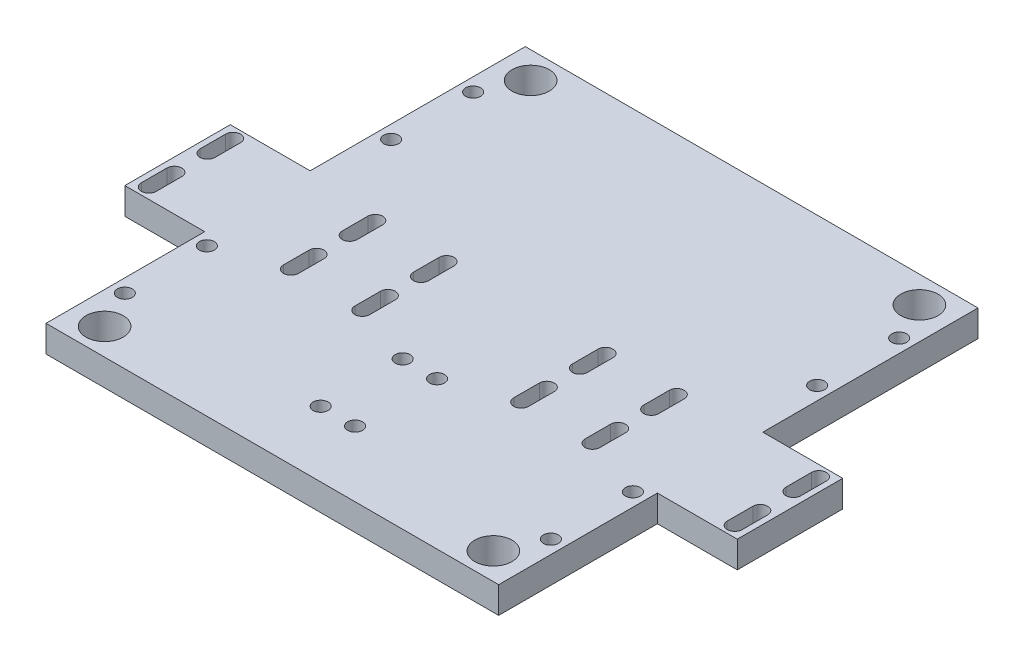
SolidWorks part; units mm, degrees
material "ABS"
ref_plane "Front Plane" through (0, 0, 0) normal (0, 0, 1) x (1, 0, 0)
ref_plane "Top Plane" through (0, 0, 0) normal (0, 1, 0) x (1, 0, 0)
ref_plane "Right Plane" through (0, 0, 0) normal (1, 0, 0) x (0, 0, -1)
sketch "Esquisse1" plane through (0, 0, 0) normal (0, 1, 0) x (1, 0, 0)
  line L0 (0, 0) -> (53.975, 0)
  line L1 (0, 0) -> (0, -114.3)
  line L2 (53.975, 0) -> (53.975, -51.308)
  line L3 (0, -114.3) -> (53.975, -114.3)
  line L4 (53.975, -76.454) -> (53.975, -114.3)
  line L5 (53.975, -51.308) -> (73.025, -51.308)
  line L7 (53.975, -76.454) -> (73.025, -76.454)
  line L8 (73.025, -51.308) -> (73.025, -76.454)
  dimension "D1" = 53.975
  dimension "D2" = 114.3
  dimension "D3" = 114.3
  dimension "D4" = 37.846
  dimension "D5" = 62.992
  dimension "D6" = 19.05
extrude "Boss.-Extru.1" add sketch "Esquisse1" along normal blind 6.35
mirror "Symétrie1" about plane through (0, 0, 0) normal (1, 0, 0) of "Boss.-Extru.1"
sketch "Esquisse4" plane through (0, 6.35, 0) normal (0, 1, 0) x (1, 0, 0)
  line L0 (-34.172, -53.8071) -> (-34.172, -59.9031)
  line L5 (-17.172, -53.8071) -> (-17.172, -59.9031)
  line L10 (-37.728, -53.8071) -> (-37.728, -59.9031)
  line L11 (-37.728, -67.8071) -> (-37.728, -73.9031)
  line L14 (-34.172, -67.8071) -> (-34.172, -73.9031)
  line L15 (-20.728, -53.8071) -> (-20.728, -59.9031)
  line L18 (0, -3.4925) -> (0, 3.4925) construction
  line L19 (-20.728, -67.8071) -> (-20.728, -73.9031)
  line L20 (-17.172, -67.8071) -> (-17.172, -73.9031)
  line L21 (17.172, -67.8071) -> (17.172, -73.9031)
  line L22 (20.728, -67.8071) -> (20.728, -73.9031)
  line L23 (20.728, -53.8071) -> (20.728, -59.9031)
  line L24 (34.172, -67.8071) -> (34.172, -73.9031)
  line L25 (37.728, -67.8071) -> (37.728, -73.9031)
  line L26 (37.728, -53.8071) -> (37.728, -59.9031)
  line L27 (17.172, -53.8071) -> (17.172, -59.9031)
  line L28 (34.172, -53.8071) -> (34.172, -59.9031)
  line L29 (-53.975, -114.3) -> (53.975, -114.3) construction
  line L33 (-68.081, -53.8071) -> (-68.081, -59.9031)
  line L34 (-71.637, -53.8071) -> (-71.637, -59.9031)
  line L35 (-71.637, -67.8071) -> (-71.637, -73.9031)
  line L36 (-68.081, -67.8071) -> (-68.081, -73.9031)
  line L37 (-35.95, -56.8551) -> (-69.859, -56.8551) construction
  line L38 (68.081, -67.8071) -> (68.081, -73.9031)
  line L39 (71.637, -67.8071) -> (71.637, -73.9031)
  line L40 (71.637, -53.8071) -> (71.637, -59.9031)
  line L41 (68.081, -53.8071) -> (68.081, -59.9031)
  circle A0 centre (-50.8, -15.621) radius 1.778
  circle A1 centre (-50.8, -35.179) radius 1.778
  circle A2 centre (50.8, -15.621) radius 1.778
  circle A3 centre (50.8, -35.179) radius 1.778
  circle A4 centre (-4.1, -98.679) radius 1.778
  circle A5 centre (4.1, -98.679) radius 1.778
  circle A6 centre (4.1, -79.121) radius 1.778
  circle A7 centre (-4.1, -79.121) radius 1.778
  circle A8 centre (-50.8, -98.679) radius 1.778
  circle A9 centre (-50.8, -79.121) radius 1.778
  circle A10 centre (50.8, -98.679) radius 1.778
  circle A11 centre (50.8, -79.121) radius 1.778
  arc A40 (-34.172, -53.8071) -> (-37.728, -53.8071) centre (-35.95, -53.8071) ccw
  arc A41 (-37.728, -59.9031) -> (-34.172, -59.9031) centre (-35.95, -59.9031) ccw
  arc A42 (-34.172, -67.8071) -> (-37.728, -67.8071) centre (-35.95, -67.8071) ccw
  arc A43 (-37.728, -73.9031) -> (-34.172, -73.9031) centre (-35.95, -73.9031) ccw
  arc A44 (-20.728, -59.9031) -> (-17.172, -59.9031) centre (-18.95, -59.9031) ccw
  arc A45 (-17.172, -53.8071) -> (-20.728, -53.8071) centre (-18.95, -53.8071) ccw
  arc A46 (-17.172, -67.8071) -> (-20.728, -67.8071) centre (-18.95, -67.8071) ccw
  arc A47 (-20.728, -73.9031) -> (-17.172, -73.9031) centre (-18.95, -73.9031) ccw
  arc A48 (20.728, -73.9031) -> (17.172, -73.9031) centre (18.95, -73.9031) cw
  arc A49 (17.172, -67.8071) -> (20.728, -67.8071) centre (18.95, -67.8071) cw
  arc A50 (17.172, -53.8071) -> (20.728, -53.8071) centre (18.95, -53.8071) cw
  arc A51 (20.728, -59.9031) -> (17.172, -59.9031) centre (18.95, -59.9031) cw
  arc A52 (37.728, -73.9031) -> (34.172, -73.9031) centre (35.95, -73.9031) cw
  arc A53 (34.172, -67.8071) -> (37.728, -67.8071) centre (35.95, -67.8071) cw
  arc A54 (37.728, -59.9031) -> (34.172, -59.9031) centre (35.95, -59.9031) cw
  arc A55 (34.172, -53.8071) -> (37.728, -53.8071) centre (35.95, -53.8071) cw
  arc A56 (-68.081, -53.8071) -> (-71.637, -53.8071) centre (-69.859, -53.8071) ccw
  arc A57 (-71.637, -59.9031) -> (-68.081, -59.9031) centre (-69.859, -59.9031) ccw
  arc A58 (-68.081, -67.8071) -> (-71.637, -67.8071) centre (-69.859, -67.8071) ccw
  arc A59 (-71.637, -73.9031) -> (-68.081, -73.9031) centre (-69.859, -73.9031) ccw
  arc A60 (71.637, -73.9031) -> (68.081, -73.9031) centre (69.859, -73.9031) cw
  arc A61 (68.081, -67.8071) -> (71.637, -67.8071) centre (69.859, -67.8071) cw
  arc A62 (71.637, -59.9031) -> (68.081, -59.9031) centre (69.859, -59.9031) cw
  arc A63 (68.081, -53.8071) -> (71.637, -53.8071) centre (69.859, -53.8071) cw
  point P37 (-35.95, -70.8551)
  point P40 (-35.95, -56.8551)
  point P48 (-18.95, -56.8551)
  point P49 (-18.95, -70.8551)
  point P94 (18.95, -70.8551)
  point P95 (18.95, -56.8551)
  point P96 (35.95, -56.8551)
  point P97 (35.95, -70.8551)
  point P107 (-69.859, -70.8551)
  point P110 (-69.859, -56.8551)
  point P128 (69.859, -56.8551)
  point P129 (69.859, -70.8551)
  dimension "D1" = 3.556
  dimension "D2" = 3.556
  dimension "D3" = 3.556
  dimension "D4" = 3.556
  dimension "D5" = 3.048
  dimension "D6" = 3.048
  dimension "D9" = 3.048
  dimension "D10" = 3.048
  dimension "D11" = 3.556
  dimension "D12" = 3.556
  dimension "D13" = 3.048
  dimension "D17" = 60.4929
  dimension "D8" = 3.048
  dimension "D14" = 3.048
  dimension "D15" = 3.048
  dimension "D16" = 40.3969
  dimension "D18" = 19.558
  dimension "D22" = 33.909
  dimension "D21" = 2
extrude "Enlèv. mat.-Extru.2" cut sketch "Esquisse4" against normal through all
sketch "Esquisse7" plane through (0, 6.35, 0) normal (0, 1, 0) x (1, 0, 0)
  line L0 (-53.975, -114.3) -> (-53.975, -76.454) construction
  line L1 (-53.975, -114.3) -> (53.975, -114.3) construction
  line L2 (53.975, -114.3) -> (53.975, -76.454) construction
  line L3 (53.975, -51.308) -> (53.975, 0) construction
  line L4 (53.975, 0) -> (-53.975, 0) construction
  line L5 (-53.975, -51.308) -> (-53.975, 0) construction
  circle A0 centre (-46.355, -6.35) radius 4.445
  circle A1 centre (46.355, -6.35) radius 4.445
  circle A2 centre (-46.355, -107.95) radius 4.445
  circle A3 centre (46.355, -107.95) radius 4.445
  dimension "D1" = 8.89
  dimension "D2" = 8.89
  dimension "D3" = 8.89
  dimension "D4" = 8.89
  dimension "D5" = 7.62
  dimension "D6" = 6.35
  dimension "D7" = 7.62
  dimension "D8" = 6.35
  dimension "D9" = 7.62
  dimension "D10" = 6.35
  dimension "D11" = 6.35
  dimension "D12" = 7.62
extrude "Enlèv. mat.-Extru.3" cut sketch "Esquisse7" against normal through all
